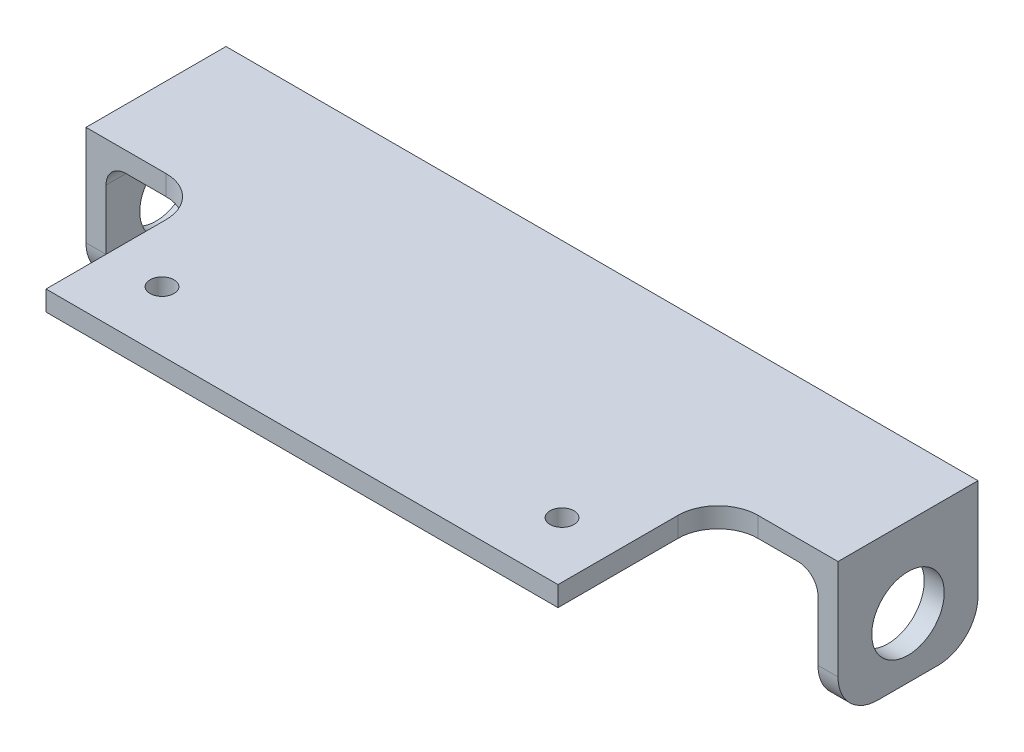
SolidWorks part; units mm, degrees
material "Delrin"
ref_plane "Front Plane" through (0, 0, 0) normal (0, 0, 1) x (1, 0, 0)
ref_plane "Top Plane" through (0, 0, 0) normal (0, 1, 0) x (1, 0, 0)
ref_plane "Right Plane" through (0, 0, 0) normal (1, 0, 0) x (0, 0, -1)
sketch "Sketch1" plane through (0, 0, 0) normal (0, 1, 0) x (1, 0, 0)
  line L0 (0, -30.8787) -> (0, 31.1298) construction
  line L1 (-15.24, -7.9375) -> (-5.715, -7.9375)
  line L2 (-18.415, -4.7625) -> (-18.415, 4.7625)
  line L3 (-15.24, 7.9375) -> (-5.715, 7.9375)
  line L4 (-2.54, -4.7625) -> (-2.54, 4.7625)
  line L5 (15.24, -11.1125) -> (-15.24, -11.1125)
  line L6 (-21.59, 4.7625) -> (-21.59, -4.7625)
  line L7 (-15.24, 11.1125) -> (15.24, 11.1125)
  line L8 (15.24, 7.9375) -> (5.715, 7.9375)
  line L9 (2.54, -4.7625) -> (2.54, 4.7625)
  line L10 (15.24, -7.9375) -> (5.715, -7.9375)
  line L11 (18.415, -4.7625) -> (18.415, 4.7625)
  line L12 (21.59, 4.7625) -> (21.59, -4.7625)
  arc A0 (-15.24, -7.9375) -> (-18.415, -4.7625) centre (-15.24, -4.7625) cw
  arc A1 (-15.24, 7.9375) -> (-18.415, 4.7625) centre (-15.24, 4.7625) ccw
  arc A2 (-2.54, 4.7625) -> (-5.715, 7.9375) centre (-5.715, 4.7625) ccw
  arc A3 (-5.715, -7.9375) -> (-2.54, -4.7625) centre (-5.715, -4.7625) ccw
  arc A4 (-21.59, -4.7625) -> (-15.24, -11.1125) centre (-15.24, -4.7625) ccw
  arc A5 (-15.24, 11.1125) -> (-21.59, 4.7625) centre (-15.24, 4.7625) ccw
  arc A6 (15.24, 11.1125) -> (21.59, 4.7625) centre (15.24, 4.7625) cw
  arc A7 (15.24, 7.9375) -> (18.415, 4.7625) centre (15.24, 4.7625) cw
  arc A8 (2.54, 4.7625) -> (5.715, 7.9375) centre (5.715, 4.7625) cw
  arc A9 (5.715, -7.9375) -> (2.54, -4.7625) centre (5.715, -4.7625) cw
  arc A10 (15.24, -7.9375) -> (18.415, -4.7625) centre (15.24, -4.7625) ccw
  arc A11 (21.59, -4.7625) -> (15.24, -11.1125) centre (15.24, -4.7625) cw
  point P9 (-18.415, -7.9375)
  point P12 (-18.415, 7.9375)
  point P17 (-2.54, -7.9375)
  point P29 (0, 11.1125)
  point P42 (0, -11.1125)
  dimension "D5" = 3.175
  dimension "D9" = 6.35
  dimension "D1" = 15.875
  dimension "D2" = 15.875
  dimension "D3" = 7.9375
  dimension "D4" = 2.54
extrude "Extrude1" add sketch "Sketch1" along normal blind 25.4 and the other way blind 50.8
sketch "Sketch2" plane through (0, 25.4, 0) normal (0, 1, 0) x (-1, 0, 0)
  line L0 (-15.24, -11.1125) -> (15.24, -11.1125) construction
  line L2 (59.69, -11.1125) -> (-59.69, -11.1125)
  line L4 (59.69, -11.1125) -> (59.69, 11.1125)
  line L8 (59.69, 11.1125) -> (-59.69, 11.1125)
  line L9 (-59.69, -11.1125) -> (-59.69, 11.1125)
  line L10 (15.24, 11.1125) -> (-15.24, 11.1125) construction
  line L11 (21.59, -4.7625) -> (21.59, 4.7625) construction
  line L12 (-21.59, 4.7625) -> (-21.59, -4.7625) construction
  dimension "D1" = 38.1
  dimension "D2" = 38.1
extrude "Extrude2" add sketch "Sketch2" along normal blind 3.175
sketch "Sketch3" plane through (0, 25.4, 0) normal (0, -1, 0) x (1, 0, 0)
  line L0 (-15.24, -11.1125) -> (-59.69, -11.1125) construction
  line L1 (-59.69, 11.1125) -> (-56.515, 11.1125)
  line L2 (-59.69, 11.1125) -> (-59.69, -11.1125)
  line L3 (-59.69, -11.1125) -> (-56.515, -11.1125)
  line L4 (-56.515, 11.1125) -> (-56.515, -11.1125)
  line L5 (59.69, 11.1125) -> (59.69, -11.1125) construction
  line L6 (59.69, 11.1125) -> (56.515, 11.1125)
  line L7 (59.69, 11.1125) -> (59.69, -11.1125)
  line L8 (59.69, -11.1125) -> (56.515, -11.1125)
  line L9 (56.515, 11.1125) -> (56.515, -11.1125)
  line L10 (59.69, -11.1125) -> (15.24, -11.1125) construction
  line L11 (15.24, 11.1125) -> (59.69, 11.1125) construction
  dimension "D1" = 3.175
  dimension "D2" = 3.175
extrude "Extrude3" add sketch "Sketch3" along normal blind 19.05
hole_wizard "Tap Drill for 1/2 Tap1" positions "3DSketch1" profile "Sketch4" hole size "1/2-20" standard "Ansi Inch"
sketch3d "3DSketch1"
  line L0 (59.69, 28.575, 11.1125) -> (59.69, 28.575, -11.1125) construction
  line L1 (-59.69, 28.575, -11.1125) -> (-59.69, 28.575, 11.1125) construction
  line L2 (-59.69, 28.575, 11.1125) -> (-59.69, 6.35, 11.1125) construction
  line L5 (59.69, 28.575, -11.1125) -> (59.69, 6.35, -11.1125) construction
  point P0 (-59.69, 15.875, 0)
  point P2 (59.69, 15.875, 0)
  dimension "D1" = 12.7
  dimension "D2" = 12.7
  dimension "D3" = 11.1125
  dimension "D4" = 11.1125
sketch "Sketch4" plane through (-59.69, 15.875, 0) normal (0, 1, 0) x (0, 0, 1)
  line L0 (0, 0) -> (0, 9.8076)
  line L1 (0, 9.8076) -> (5.7544, 6.35)
  line L2 (5.7544, 6.35) -> (5.7544, 0)
  line L5 (5.7544, 0) -> (0, 0)
  line L10 (0, 9.8076) -> (-5.7544, 6.35) construction
  line L11 (0, -6.35) -> (0, 107.95) construction
  dimension "Hole Dia." = 11.5087
  dimension "Hole Depth" = 6.35
  dimension "Drill Angle" = 118
hole_wizard "#8 Clearance Hole1" positions "3DSketch2" profile "Sketch5" hole size "#8" standard "Ansi Inch"
sketch3d "3DSketch2"
  line L2 (-21.59, 25.4, -4.7625) -> (-21.59, -50.8, -4.7625) construction
  line L3 (21.59, 25.4, 4.7625) -> (21.59, -50.8, 4.7625) construction
  point P0 (-21.59, 15.875, 0)
  point P2 (-21.59, 15.875, 0)
  point P4 (21.59, 15.875, 0)
  dimension "D1" = 12.7
  dimension "D2" = 12.7
  dimension "D3" = 4.7625
  dimension "D4" = 4.7625
sketch "Sketch5" plane through (-21.59, 15.875, 0) normal (0, 1, 0) x (0, 0, 1)
  line L0 (0, 0) -> (0, 7.7007)
  line L1 (0, 7.7007) -> (2.2479, 6.35)
  line L2 (2.2479, 6.35) -> (2.2479, 0)
  line L5 (2.2479, 0) -> (0, 0)
  line L10 (0, 7.7007) -> (-2.2479, 6.35) construction
  line L11 (0, -6.35) -> (0, 107.95) construction
  dimension "Hole Dia." = 4.4958
  dimension "Hole Depth" = 6.35
  dimension "Drill Angle" = 118
fillet "Fillet1" radius 6.35 4 edges at (-58.1025, 6.35, 11.1125) (-58.1025, 6.35, -11.1125) (58.1025, 6.35, -11.1125) (58.1025, 6.35, 11.1125)
fillet "Fillet3" radius 3.175 2 edges at (-56.515, 25.4, 0) (56.515, 25.4, 0)
sketch "Sketch7" plane through (0, 0, 11.1125) normal (0, 0, 1) x (1, 0, 0)
  line L0 (-59.69, 28.575) -> (59.69, 28.575) construction
  line L1 (-40.64, 28.575) -> (40.64, 28.575)
  line L2 (-40.64, 28.575) -> (-40.64, 25.4)
  line L3 (-40.64, 25.4) -> (40.64, 25.4)
  line L4 (40.64, 28.575) -> (40.64, 25.4)
  line L5 (15.24, 25.4) -> (53.34, 25.4) construction
  line L6 (-59.69, 28.575) -> (-59.69, 12.7) construction
  line L7 (59.69, 28.575) -> (59.69, 12.7) construction
  dimension "D1" = 19.05
  dimension "D2" = 19.05
extrude "Extrude4" add sketch "Sketch7" along normal blind 25.4
fillet "Fillet4" radius 6.35 2 edges at (-40.64, 26.9875, 11.1125) (40.64, 26.9875, 11.1125)
hole_wizard "#6 Clearance Hole1" positions "3DSketch3" profile "Sketch6" hole size "#6" standard "Ansi Inch"
sketch3d "3DSketch3"
  line L9 (40.64, 28.575, 26.9875) -> (-40.64, 28.575, 26.9875) construction
  line L10 (40.64, 28.575, 36.5125) -> (40.64, 28.575, 17.4625) construction
  line L11 (-40.64, 28.575, 36.5125) -> (-40.64, 28.575, 17.4625) construction
  line L13 (0, 28.575, -11.1125) -> (0, 28.575, 36.5125) construction
  line L14 (59.69, 28.575, -11.1125) -> (-59.69, 28.575, -11.1125) construction
  line L15 (40.64, 28.575, 36.5125) -> (-40.64, 28.575, 36.5125) construction
  point P0 (31.75, 28.575, 26.9875)
  point P2 (-31.75, 28.575, 26.9875)
  dimension "D1" = 63.5
  dimension "D2" = 31.75
sketch "Sketch6" plane through (31.75, 28.575, 26.9875) normal (1, 0, 0) x (0, 0, 1)
  line L0 (0, 0) -> (0, 10.7928)
  line L1 (0, 10.7928) -> (1.8986, 9.652)
  line L2 (1.8986, 9.652) -> (1.8986, 0)
  line L5 (1.8986, 0) -> (0, 0)
  line L10 (0, 10.7928) -> (-1.8987, 9.652) construction
  line L11 (0, -6.35) -> (0, 107.95) construction
  dimension "Hole Dia." = 3.7973
  dimension "Hole Depth" = 9.652
  dimension "Drill Angle" = 118
sketch "Sketch8" plane through (0, -50.8, 0) normal (0, -1, 0) x (1, 0, 0)
  line L1 (-33.2007, 26.7746) -> (33.1381, 26.7746)
  line L2 (-33.2007, 26.7746) -> (-33.2007, -34.3669)
  line L3 (-33.2007, -34.3669) -> (33.1381, -34.3669)
  line L4 (33.1381, 26.7746) -> (33.1381, -34.3669)
extrude "Cut-Extrude1" cut sketch "Sketch8" against normal blind 57.15
sketch "Sketch10" plane through (0, 28.575, 0) normal (0, 1, 0) x (1, 0, 0)
  line L16 (-57.15, 8.5725) -> (-57.15, -8.5725)
  line L17 (-57.15, -8.5725) -> (-46.99, -8.5725)
  line L18 (-38.1, -17.4625) -> (-38.1, -33.9725)
  line L19 (-38.1, -33.9725) -> (38.1, -33.9725)
  line L20 (38.1, -33.9725) -> (38.1, -17.4625)
  line L21 (46.99, -8.5725) -> (57.15, -8.5725)
  line L22 (57.15, -8.5725) -> (57.15, 8.5725)
  line L23 (57.15, 8.5725) -> (-57.15, 8.5725)
  line L24 (-57.15, 8.5725) -> (-57.15, -8.5725)
  line L25 (-57.15, -8.5725) -> (-46.99, -8.5725)
  line L26 (-38.1, -17.4625) -> (-38.1, -33.9725)
  line L27 (-38.1, -33.9725) -> (38.1, -33.9725)
  line L28 (38.1, -33.9725) -> (38.1, -17.4625)
  line L29 (46.99, -8.5725) -> (57.15, -8.5725)
  line L30 (57.15, -8.5725) -> (57.15, 8.5725)
  line L31 (57.15, 8.5725) -> (-57.15, 8.5725)
  arc A4 (-38.1, -17.4625) -> (-46.99, -8.5725) centre (-46.99, -17.4625) ccw
  arc A5 (46.99, -8.5725) -> (38.1, -17.4625) centre (46.99, -17.4625) ccw
  arc A6 (-38.1, -17.4625) -> (-46.99, -8.5725) centre (-46.99, -17.4625) ccw
  arc A7 (46.99, -8.5725) -> (38.1, -17.4625) centre (46.99, -17.4625) ccw
  dimension "D1" = 2.54
sketch "Sketch11" plane through (0, 25.4, 0) normal (0, -1, 0) x (1, 0, 0)
  point P0 (31.75, 26.9875)
  point P1 (-31.75, 26.9875)
